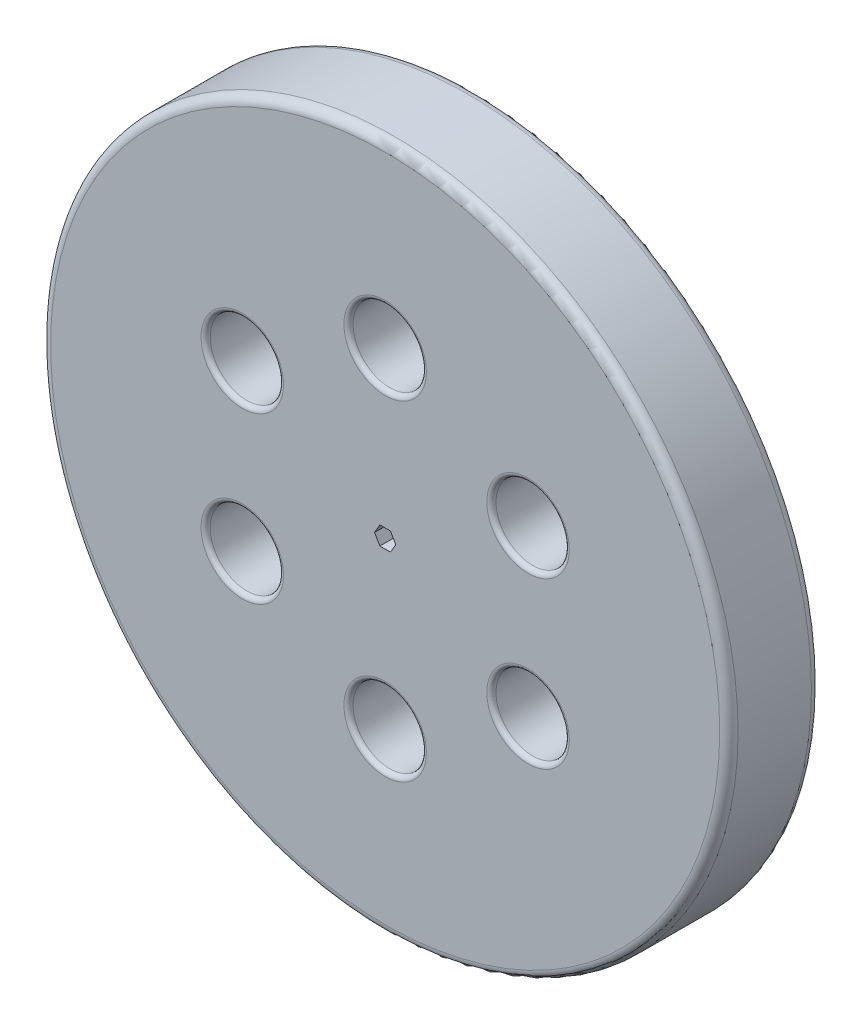
SolidWorks part; units mm, degrees
material "ABS"
ref_plane "Front" through (0, 0, 0) normal (0, 0, 1) x (1, 0, 0)
ref_plane "Top" through (0, 0, 0) normal (0, 1, 0) x (1, 0, 0)
ref_plane "Right" through (0, 0, 0) normal (1, 0, 0) x (0, 0, -1)
sketch "Sketch1" plane through (0, 0, 0) normal (0, 0, 1) x (1, 0, 0)
  circle A0 centre (0, 0) radius 37.5
  dimension "D1" = 75
extrude "Boss-Extrude1" add sketch "Sketch1" along normal blind 10
sketch "Sketch2" plane through (0, 0, 10) normal (0, 0, 1) x (1, 0, 0)
  line L1 (1.1547, 0) -> (0.5774, 1)
  line L2 (0.5774, 1) -> (-0.5774, 1)
  line L3 (-0.5774, 1) -> (-1.1547, 0)
  line L4 (-1.1547, 0) -> (-0.5774, -1)
  line L5 (-0.5774, -1) -> (0.5774, -1)
  line L6 (0.5774, -1) -> (1.1547, 0)
  circle A1 centre (0, 0) radius 1 construction
  dimension "D1" = 2
sketch "Sketch3" plane through (0, 0, 10) normal (0, 0, 1) x (1, 0, 0)
  circle A0 centre (0, 18) radius 4
  dimension "D1" = 8
  dimension "D2" = 18
extrude "Cut-Extrude3" cut sketch "Sketch3" against normal through all
pattern_circular "CirPattern1" count 6 over 360 about axis through (0, 0, 0) along (0, 0, 1) of "Cut-Extrude3"
fillet "Fillet1" radius 1 2 edges at (37.5, 0, 0) (37.5, 0, 10)
fillet "Fillet2" radius 0.5 12 edges at (-17.5885, -5.5359, 10) (-17.5885, -5.5359, 0) (-4, -18, 0) (-4, -18, 10) (13.5885, -12.4641, 10) (13.5885, -12.4641, 0) (17.5885, 5.5359, 0) (17.5885, 5.5359, 10) (4, 18, 10) (4, 18, 0) (-13.5885, 12.4641, 0) (-13.5885, 12.4641, 10)
extrude "Cut-Extrude4" cut sketch "Sketch2" against normal up to surface (10 mm away) up to face at (-11.0885, -9, 0)
